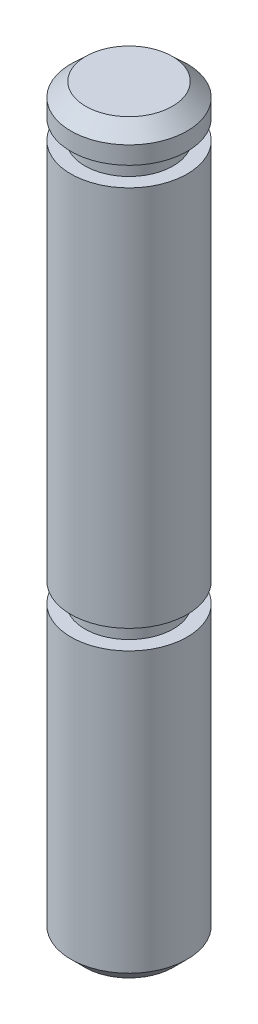
SolidWorks part; units mm, degrees
ref_plane "Front Plane" through (0, 0, 0) normal (0, 0, 1) x (1, 0, 0)
ref_plane "Top Plane" through (0, 0, 0) normal (0, 1, 0) x (1, 0, 0)
ref_plane "Right Plane" through (0, 0, 0) normal (1, 0, 0) x (0, 0, -1)
sketch "Sketch2" plane through (0, 0, 0) normal (0, 0, 1) x (1, 0, 0)
  line L0 (0, 0) -> (0, 17.0045) construction
  line L1 (-1.5875, -5.207) -> (-1.5875, 5.207)
  line L2 (-1.5875, 5.207) -> (-1.2065, 5.207)
  line L3 (-1.2065, 5.207) -> (-1.2065, 5.7404)
  line L4 (-1.2065, 5.7404) -> (-1.5875, 5.7404)
  line L5 (-1.5875, 5.7404) -> (-1.5875, 6.223)
  line L6 (-1.5875, 6.223) -> (-1.1828, 6.604)
  line L7 (-1.1828, 6.604) -> (0, 6.604)
  line L8 (0, 6.604) -> (0, -6.604)
  line L9 (0, 0) -> (-14.3814, 0) construction
  line L10 (-1.5875, -5.7404) -> (-1.5875, -13.3604)
  line L11 (-1.5875, -13.3604) -> (-1.2065, -13.7414)
  line L12 (-1.2065, -13.7414) -> (0, -13.7414)
  line L13 (-1.2065, -5.7404) -> (-1.5875, -5.7404)
  line L14 (-1.2065, -5.207) -> (-1.2065, -5.7404)
  line L15 (-1.5875, -5.207) -> (-1.2065, -5.207)
  line L16 (0, -13.7414) -> (0, -6.604)
  point P19 (-1.5875, 0)
  dimension "D1" = 3.175
  dimension "D2" = 2.413
  dimension "D3" = 3.175
  dimension "D4" = 3.175
  dimension "D5" = 0.5334
  dimension "D6" = 5.207
  dimension "D7" = 6.604
  dimension "D8" = 0.381
  dimension "D9" = 7.62
  dimension "D10" = 45
  dimension "D11" = 0.381
revolve "Revolve4" add sketch "Sketch2" angle 360 about L0
